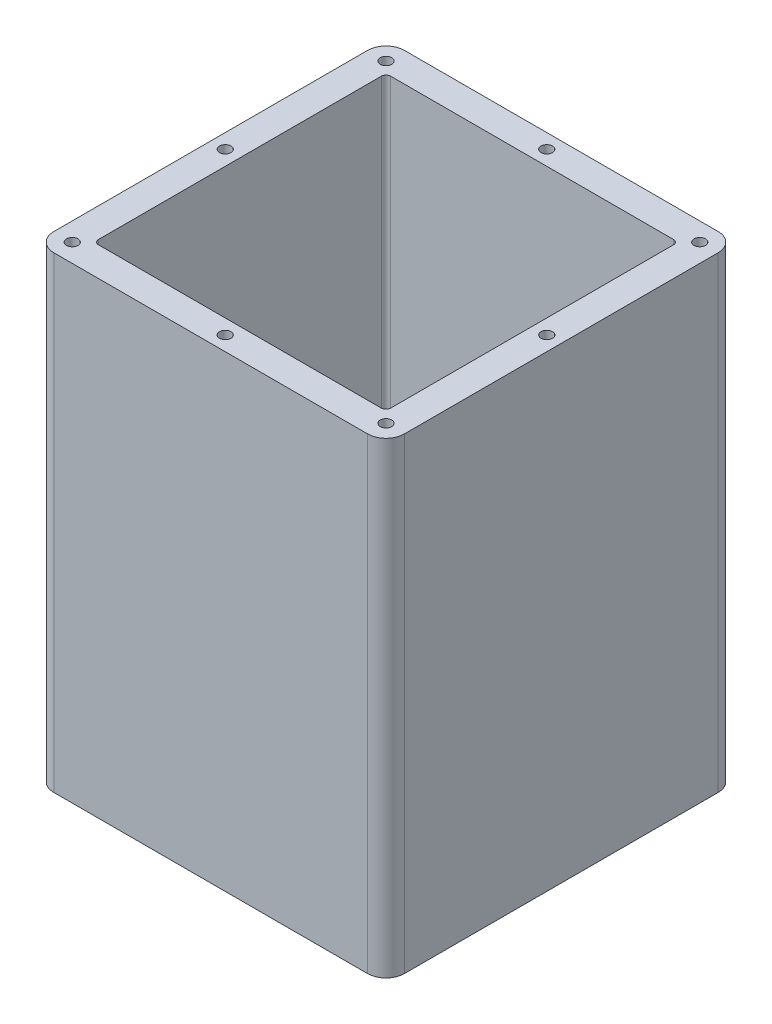
SolidWorks part; units mm, degrees
ref_plane "Front Plane" through (0, 0, 0) normal (0, 0, 1) x (1, 0, 0)
ref_plane "Top Plane" through (0, 0, 0) normal (0, 1, 0) x (1, 0, 0)
ref_plane "Right Plane" through (0, 0, 0) normal (1, 0, 0) x (0, 0, -1)
sketch "Sketch1" plane through (0, 0, 0) normal (0, 1, 0) x (1, 0, 0)
  line L1 (-35.56, -38.1) -> (35.56, -38.1)
  line L2 (-38.1, -35.56) -> (-38.1, 35.56)
  line L3 (-35.56, 38.1) -> (35.56, 38.1)
  line L4 (38.1, -35.56) -> (38.1, 35.56)
  line L5 (-38.1, -38.1) -> (38.1, 38.1) construction
  line L6 (-38.1, 38.1) -> (38.1, -38.1) construction
  arc A0 (-35.56, -38.1) -> (-38.1, -35.56) centre (-35.56, -35.56) cw
  arc A1 (35.56, -38.1) -> (38.1, -35.56) centre (35.56, -35.56) ccw
  arc A2 (35.56, 38.1) -> (38.1, 35.56) centre (35.56, 35.56) cw
  arc A3 (-38.1, 35.56) -> (-35.56, 38.1) centre (-35.56, 35.56) cw
  point P0 (0, 0)
  dimension "D3" = 2.54
  dimension "D1" = 76.2
  dimension "D2" = 76.2
extrude "Boss-Extrude1" add sketch "Sketch1" along normal blind 101.604
sketch "Sketch9" plane through (0, 101.604, 0) normal (0, 1, 0) x (1, 0, 0)
  line L0 (35.56, 38.1) -> (-35.56, 38.1) construction
  line L1 (-30.56, -33.1) -> (30.56, -33.1)
  line L2 (-33.1, -30.56) -> (-33.1, 30.56)
  line L3 (-30.56, 33.1) -> (30.56, 33.1)
  line L4 (33.1, -30.56) -> (33.1, 30.56)
  line L5 (-33.1, -33.1) -> (33.1, 33.1) construction
  line L6 (-33.1, 33.1) -> (33.1, -33.1) construction
  line L7 (38.1, -35.56) -> (38.1, 35.56) construction
  arc A0 (-30.56, -33.1) -> (-33.1, -30.56) centre (-30.56, -30.56) cw
  arc A1 (30.56, -33.1) -> (33.1, -30.56) centre (30.56, -30.56) ccw
  arc A2 (30.56, 33.1) -> (33.1, 30.56) centre (30.56, 30.56) cw
  arc A3 (-33.1, 30.56) -> (-30.56, 33.1) centre (-30.56, 30.56) cw
  point P0 (0, 0)
  dimension "D3" = 2.54
  dimension "D1" = 5
  dimension "D2" = 5
extrude "Cut-Extrude1" cut sketch "Sketch9" against normal blind 246.126
sketch "Sketch13" plane through (0, 0, -33.1) normal (0, 0, 1) x (1, 0, 0)
  line L1 (-20, 36.007) -> (20, 36.007)
  line L2 (-20, 36.007) -> (-20, 76.007)
  line L3 (-20, 76.007) -> (20, 76.007)
  line L4 (20, 36.007) -> (20, 76.007)
  line L5 (-20, 36.007) -> (20, 76.007) construction
  line L6 (-20, 76.007) -> (20, 36.007) construction
  point P0 (0, 56.007)
  dimension "D1" = 40
  dimension "D2" = 40
sketch "Sketch14" plane through (0, 101.604, 0) normal (0, 1, 0) x (1, 0, 0)
  line L2 (-38.1, -38.1) -> (38.1, -38.1)
  line L4 (-38.1, -38.1) -> (-38.1, 38.1)
  line L5 (-31.75, 31.75) -> (31.75, 31.75)
  line L6 (-31.75, 31.75) -> (-31.75, -31.75)
  line L7 (-31.75, -31.75) -> (31.75, -31.75)
  line L8 (31.75, 31.75) -> (31.75, -31.75)
  line L9 (-31.75, 31.75) -> (31.75, -31.75) construction
  line L10 (-31.75, -31.75) -> (31.75, 31.75) construction
  line L11 (-38.1, 38.1) -> (38.1, 38.1)
  line L12 (38.1, -38.1) -> (38.1, 38.1)
  line L13 (-38.1, -38.1) -> (38.1, 38.1) construction
  line L14 (-38.1, 38.1) -> (38.1, -38.1) construction
  point P0 (0, 0)
  point P9 (0, 0)
extrude "Boss-Extrude3" add sketch "Sketch14" against normal blind 101.604
fillet "Fillet1" radius 4 4 edges at (-38.1, 50.802, -38.1) (-38.1, 50.802, 38.1) (38.1, 50.802, 38.1) (38.1, 50.802, -38.1)
hole_wizard "M3x0.5 Tapped Hole2" positions "Sketch17" profile "Sketch18" tap size "M3x0.5" standard "ANSI Metric"
sketch "Sketch17" plane through (0, 101.604, 0) normal (0, 1, 0) x (1, 0, 0)
  point P0 (-34.1, 34.1)
  point P3 (34.1, 34.1)
  point P6 (34.1, -34.1)
  point P9 (-34.1, -34.1)
  point P21 (-34.95, 0)
  point P24 (34.95, 0)
  point P27 (0, -34.95)
  point P30 (0, 34.95)
sketch "Sketch18" plane through (-34.1, 101.604, -34.1) normal (1, 0, 0) x (0, 0, 1)
  line L0 (0, 0) -> (0, 8.2511)
  line L1 (0, 8.2511) -> (1.25, 7.5)
  line L2 (1.25, 7.5) -> (1.25, 0)
  line L5 (1.25, 0) -> (0, 0)
  line L10 (0, 8.2511) -> (-1.25, 7.5) construction
  line L11 (0, -6.35) -> (0, 107.95) construction
  dimension "Tap Drill Dia." = 2.5
  dimension "Tap Drill Depth" = 7.5
  dimension "Drill Angle" = 118
sketch "Sketch21" plane through (38.1, 0, 0) normal (1, 0, 0) x (0, 0, -1)
  circle A0 centre (0, 76.708) radius 10
  circle A1 centre (0, 33.7027) radius 10
  dimension "D2" = 20
  dimension "D3" = 20
hole_wizard "M3x0.5 Tapped Hole1" positions "Sketch24" profile "Sketch23" tap size "M3x0.5" standard "ANSI Metric"
sketch "Sketch24" plane through (0, 0, 0) normal (0, -1, 0) x (-1, 0, 0)
  point P0 (-34.1, 34.1)
  point P2 (34.1, 34.1)
  point P4 (34.1, -34.1)
  point P6 (-34.1, -34.1)
  point P16 (-34.95, 0)
  point P19 (0, 34.95)
  point P22 (34.95, 0)
  point P25 (0, -34.95)
sketch "Sketch23" plane through (34.1, 0, -34.1) normal (1, 0, 0) x (0, 0, -1)
  line L0 (0, 0) -> (0, 8.2511)
  line L1 (0, 8.2511) -> (1.25, 7.5)
  line L2 (1.25, 7.5) -> (1.25, 0)
  line L5 (1.25, 0) -> (0, 0)
  line L10 (0, 8.2511) -> (-1.25, 7.5) construction
  line L11 (0, -6.35) -> (0, 107.95) construction
  dimension "Tap Drill Dia." = 2.5
  dimension "Tap Drill Depth" = 7.5
  dimension "Drill Angle" = 118
fillet "Fillet2" radius 1 4 edges at (31.75, 50.802, 31.75) (-31.75, 50.802, 31.75) (-31.75, 50.802, -31.75) (31.75, 50.802, -31.75)
